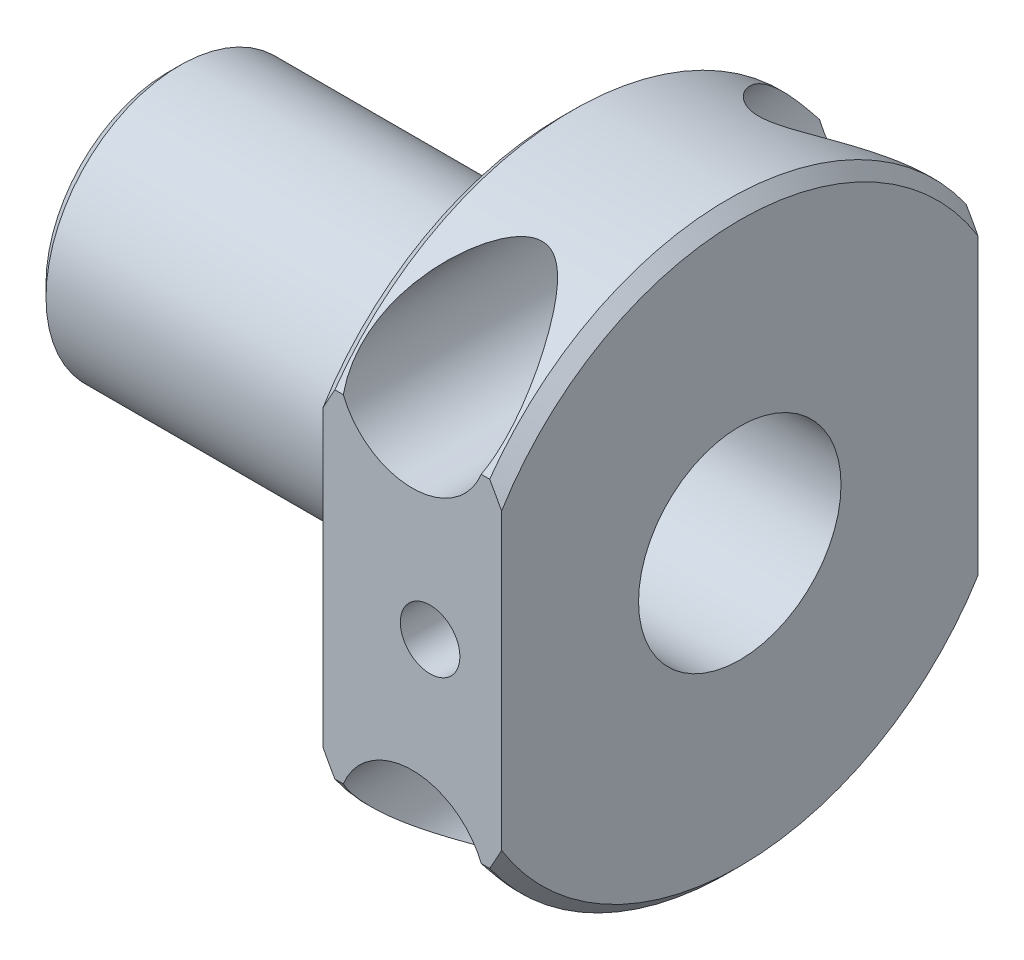
SolidWorks part; units mm, degrees
material "6061-T6 (SS)"
ref_plane "Front Plane" through (0, 0, 0) normal (0, 0, 1) x (1, 0, 0)
ref_plane "Top Plane" through (0, 0, 0) normal (0, 1, 0) x (1, 0, 0)
ref_plane "Right Plane" through (0, 0, 0) normal (1, 0, 0) x (0, 0, -1)
sketch "Sketch1" plane through (0, 0, 0) normal (1, 0, 0) x (0, 0, -1)
  circle A0 centre (0, 0) radius 12.446
  circle A1 centre (0, 0) radius 4.318
  dimension "D1" = 24.892
  dimension "D2" = 8.636
extrude "Boss-Extrude1" add sketch "Sketch1" along normal blind 22.86
sketch "Sketch2" plane through (0, 0, 0) normal (0, 0, 1) x (1, 0, 0)
  line L0 (0, 0) -> (27.8881, 0) construction
  line L1 (22.86, -12.446) -> (22.86, 12.446) construction
  line L2 (15.24, 17.1156) -> (15.24, -16.353) construction
  line L3 (19.05, 8.382) -> (15.24, 8.382) construction
  line L4 (19.05, 8.382) -> (22.86, 8.382) construction
  circle A0 centre (19.05, 8.382) radius 3.175
  dimension "D1" = 6.35
  dimension "D3" = 8.382
  dimension "D4" = 7.62
extrude "Cut-Extrude1" cut sketch "Sketch2" against normal through all and the other way through all
mirror "Mirror1" about plane through (0, 0, 0) normal (0, 1, 0) of "Cut-Extrude1"
sketch "Sketch4" plane through (0, 0, 0) normal (-1, 0, 0) x (0, 0, 1)
  circle A0 centre (0, 0) radius 5.715
  circle A1 centre (0, 0) radius 25.4
  dimension "D1" = 50.8
  dimension "D2" = 11.43
extrude "Cut-Extrude3" cut sketch "Sketch4" against normal blind 15.24
ref_plane "Plane1" through (13.1826, 0, 0) normal (-1, 0, 0) x (0, 0, 1)
sketch "Sketch3" plane through (22.86, 0, 0) normal (1, 0, 0) x (0, 0, -1)
  circle A0 centre (0, 0) radius 8.255 construction
  circle A1 centre (-8.255, 0) radius 1.2827
  circle A2 centre (8.255, 0) radius 1.2827
  dimension "D1" = 16.51
  dimension "D2" = 2.5654
extrude "Cut-Extrude2" [suppressed] cut sketch "Sketch3" against normal blind 10.16
cosmetic thread "Cosmetic Thread1" [suppressed] parameters "D2"=3.175
cosmetic thread "Cosmetic Thread2" [suppressed] parameters "D2"=3.175
ref_plane "Plane2" through (0, 0, 12.7) normal (0, 0, 1) x (1, 0, 0)
ref_plane "Plane3" through (0, 0, 4.318) normal (0, 0, -1) x (-1, 0, 0)
ref_plane "Plane4" through (0, 0, 11.938) normal (0, 0, -1) x (-1, 0, 0)
sketch "Sketch7" plane through (0, 0, 11.938) normal (0, 0, -1) x (1, 0, 0)
  line L1 (22.86, -12.446) -> (22.86, 12.446) construction
  circle A0 centre (19.812, 0) radius 1.27
  dimension "D1" = 2.54
  dimension "D2" = 3.048
extrude "Cut-Extrude4" cut sketch "Sketch7" along normal blind 5.334 and the other way through all
sketch "Sketch8" plane through (0, 0, 0) normal (-1, 0, 0) x (0, 0, 1)
  circle A0 centre (0, 0) radius 4.318 construction
  circle A1 centre (0, 0) radius 5.715
  circle A2 centre (0, 0) radius 5.715
  circle A3 centre (0, 0) radius 4.318
  dimension "D1" = 0
extrude "Boss-Extrude2" add sketch "Sketch8" along normal blind 1.524
chamfer "Chamfer1" distance 0.508 angle 45 3 edges at (15.24, 0, 12.446) (22.86, 0, -12.446) (-1.524, 0, 5.715)
sketch "Sketch9" plane through (15.24, 0, 0) normal (-1, 0, 0) x (0, 0, 1)
  line L1 (10.16, -16.3103) -> (-10.16, -16.3103)
  line L2 (10.16, -16.3103) -> (10.16, 16.3103)
  line L3 (10.16, 16.3103) -> (-10.16, 16.3103)
  line L4 (-10.16, -16.3103) -> (-10.16, 16.3103)
  line L5 (10.16, -16.3103) -> (-10.16, 16.3103) construction
  line L6 (10.16, 16.3103) -> (-10.16, -16.3103) construction
  circle A0 centre (0, 0) radius 23.6117
  point P0 (0, 0)
  dimension "D1" = 20.32
extrude "Cut-Extrude5" cut sketch "Sketch9" against normal blind 13.97
